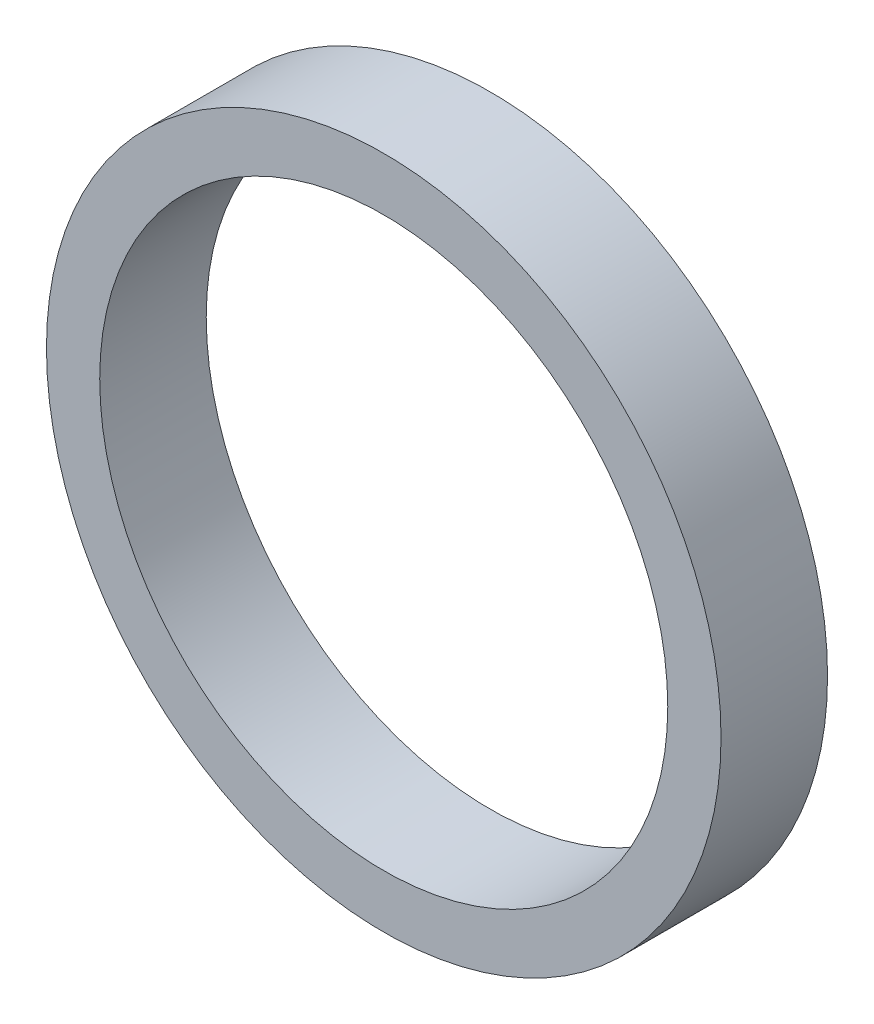
SolidWorks part; units mm, degrees
material "Aluminum Bronze"
ref_plane "Plan de face" through (0, 0, 0) normal (0, 0, 1) x (1, 0, 0)
ref_plane "Plan de dessus" through (0, 0, 0) normal (0, 1, 0) x (1, 0, 0)
ref_plane "Plan de droite" through (0, 0, 0) normal (1, 0, 0) x (0, 0, -1)
sketch "Sketch1" plane through (0, 0, 0) normal (0, 0, 1) x (1, 0, 0)
  circle A0 centre (0, 0) radius 8
  circle A1 centre (0, 0) radius 9.5
  dimension "D1" = 19
  dimension "D2" = 16
extrude "Boss-Extrude1" add sketch "Sketch1" along normal blind 3
